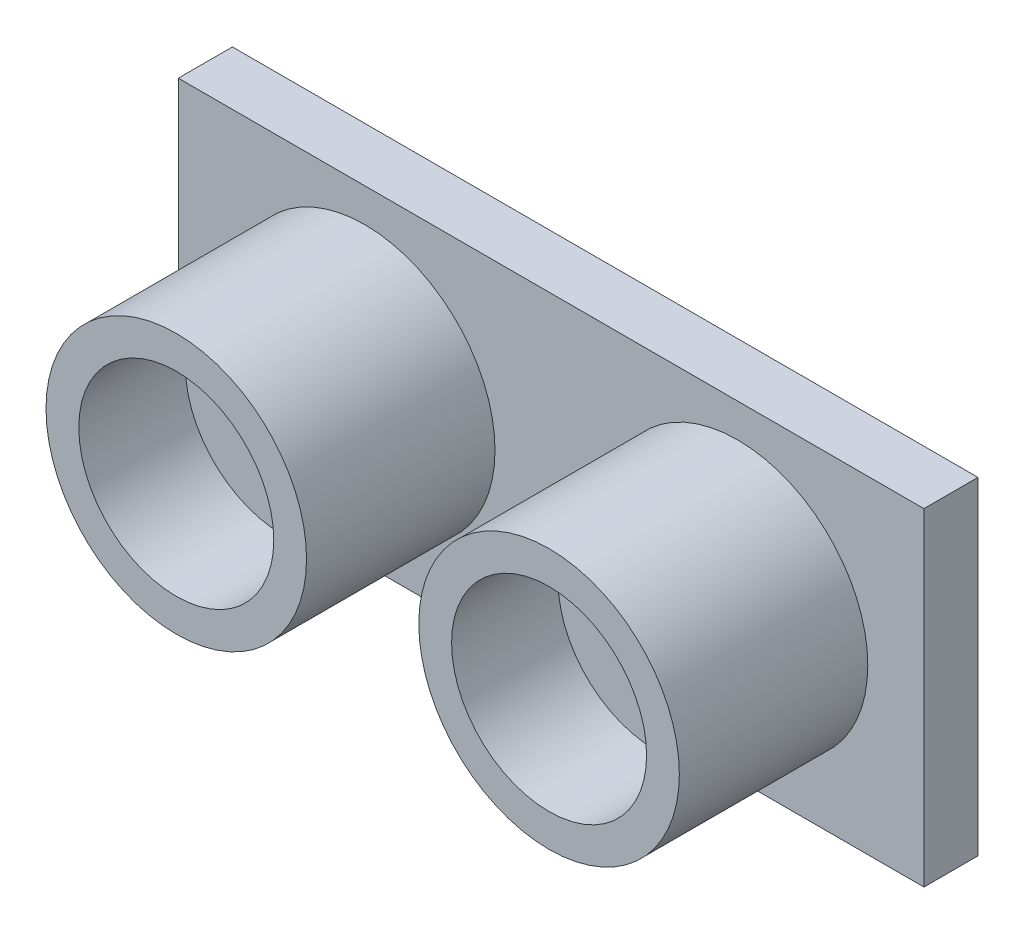
SolidWorks part; units mm, degrees
ref_plane "Alzado" through (0, 0, 0) normal (0, 0, 1) x (1, 0, 0)
ref_plane "Planta" through (0, 0, 0) normal (0, 1, 0) x (1, 0, 0)
ref_plane "Vista lateral" through (0, 0, 0) normal (1, 0, 0) x (0, 0, -1)
sketch "Croquis1" plane through (0, 0, 0) normal (0, 0, 1) x (1, 0, 0)
  line L1 (0, 0) -> (45.5, 0)
  line L2 (0, 0) -> (0, 20)
  line L3 (0, 20) -> (45.5, 20)
  line L4 (45.5, 0) -> (45.5, 20)
  dimension "D1" = 45.5
  dimension "D2" = 20
extrude "Saliente-Extruir1" add sketch "Croquis1" along normal blind 3.3
sketch "Croquis2" plane through (0, 0, 3.3) normal (0, 0, 1) x (1, 0, 0)
  line L0 (22.75, 20) -> (22.75, 0) construction
  line L1 (45.5, 20) -> (0, 20) construction
  line L2 (0, 0) -> (45.5, 0) construction
  line L3 (45.5, 10) -> (0, 10) construction
  line L4 (45.5, 0) -> (45.5, 20) construction
  line L5 (0, 20) -> (0, 0) construction
  circle A0 centre (34.125, 10) radius 7.95
  circle A1 centre (11.375, 10) radius 7.95
  dimension "D1" = 15.9
  dimension "D2" = 11.375
extrude "Saliente-Extruir2" add sketch "Croquis2" along normal blind 11.5
sketch "Croquis3" plane through (0, 0, 14.8) normal (0, 0, 1) x (1, 0, 0)
  line L0 (22.75, 20) -> (22.75, 0) construction
  line L1 (45.5, 20) -> (0, 20) construction
  line L2 (0, 0) -> (45.5, 0) construction
  circle A0 centre (34.125, 10) radius 5.95
  circle A1 centre (34.125, 10) radius 7.95 construction
  circle A2 centre (11.375, 10) radius 5.95
  dimension "D1" = 2
extrude "Cortar-Extruir1" cut sketch "Croquis3" against normal blind 6.5
sketch "Croquis4" plane through (0, 0, 0) normal (0, 0, -1) x (-1, 0, 0)
  line L0 (0, 0) -> (-45.5, 0) construction
  line L1 (-27.5, 0) -> (-17.5, 0)
  line L2 (-27.5, 0) -> (-27.5, 2.5)
  line L3 (-27.5, 2.5) -> (-17.5, 2.5)
  line L4 (-17.5, 0) -> (-17.5, 2.5)
  line L5 (0, 20) -> (0, 0) construction
  dimension "D1" = 10
  dimension "D2" = 17.5
  dimension "D3" = 2.5
extrude "Saliente-Extruir3" add sketch "Croquis4" along normal blind 2.5
sketch "Croquis5" plane through (0, 0, -2.5) normal (0, 0, -1) x (-1, 0, 0)
  line L0 (-17.5, 2.5) -> (-27.5, 2.5) construction
  line L1 (-27.435, 2.45) -> (-25.035, 2.45)
  line L2 (-27.435, 2.45) -> (-27.435, 0.05)
  line L3 (-27.435, 0.05) -> (-25.035, 0.05)
  line L4 (-25.035, 2.45) -> (-25.035, 0.05)
  line L5 (-24.945, 2.45) -> (-22.545, 2.45)
  line L6 (-24.945, 2.45) -> (-24.945, 0.05)
  line L7 (-24.945, 0.05) -> (-22.545, 0.05)
  line L8 (-22.545, 2.45) -> (-22.545, 0.05)
  line L9 (-22.455, 2.45) -> (-20.055, 2.45)
  line L10 (-22.455, 2.45) -> (-22.455, 0.05)
  line L11 (-22.455, 0.05) -> (-20.055, 0.05)
  line L12 (-20.055, 2.45) -> (-20.055, 0.05)
  line L13 (-19.965, 2.45) -> (-17.565, 2.45)
  line L14 (-19.965, 2.45) -> (-19.965, 0.05)
  line L15 (-19.965, 0.05) -> (-17.565, 0.05)
  line L16 (-17.565, 2.45) -> (-17.565, 0.05)
  line L17 (-27.5, 0) -> (-17.5, 0) construction
  line L19 (-27.5, 2.5) -> (-27.5, 0) construction
  line L20 (-17.5, 0) -> (-17.5, 2.5) construction
  dimension "D1" = 0.05
  dimension "D2" = 0.05
  dimension "D3" = 0.065
  dimension "D4" = 0.065
  dimension "D5" = 0.09
  dimension "D6" = 0.09
extrude "Saliente-Extruir4" add sketch "Croquis5" along normal blind 2
sketch "Croquis6" plane through (0, 0.05, 0) normal (0, -1, 0) x (1, 0, 0)
  line L0 (19.965, -4.5) -> (19.965, -2.5) construction
  line L1 (17.565, -4.5) -> (19.965, -4.5)
  line L2 (17.565, -4.5) -> (17.565, -3)
  line L3 (17.565, -3) -> (19.965, -3)
  line L4 (19.965, -4.5) -> (19.965, -3)
  line L5 (20.055, -4.5) -> (20.055, -2.5) construction
  line L6 (20.055, -3) -> (22.455, -3)
  line L7 (20.055, -3) -> (20.055, -4.5)
  line L8 (20.055, -4.5) -> (22.455, -4.5)
  line L9 (22.455, -3) -> (22.455, -4.5)
  line L10 (22.545, -4.5) -> (22.545, -2.5) construction
  line L11 (22.545, -3) -> (24.945, -3)
  line L12 (22.545, -3) -> (22.545, -4.5)
  line L13 (22.545, -4.5) -> (24.945, -4.5)
  line L14 (24.945, -3) -> (24.945, -4.5)
  line L15 (25.035, -4.5) -> (25.035, -2.5) construction
  line L16 (25.035, -3) -> (27.435, -3)
  line L17 (25.035, -3) -> (25.035, -4.5)
  line L18 (25.035, -4.5) -> (27.435, -4.5)
  line L19 (27.435, -3) -> (27.435, -4.5)
  line L20 (27.435, -4.5) -> (27.435, -2.5) construction
  line L21 (27.435, -4.5) -> (25.035, -4.5) construction
  dimension "D1" = 1.5
extrude "Saliente-Extruir5" add sketch "Croquis6" along normal blind 5.3
